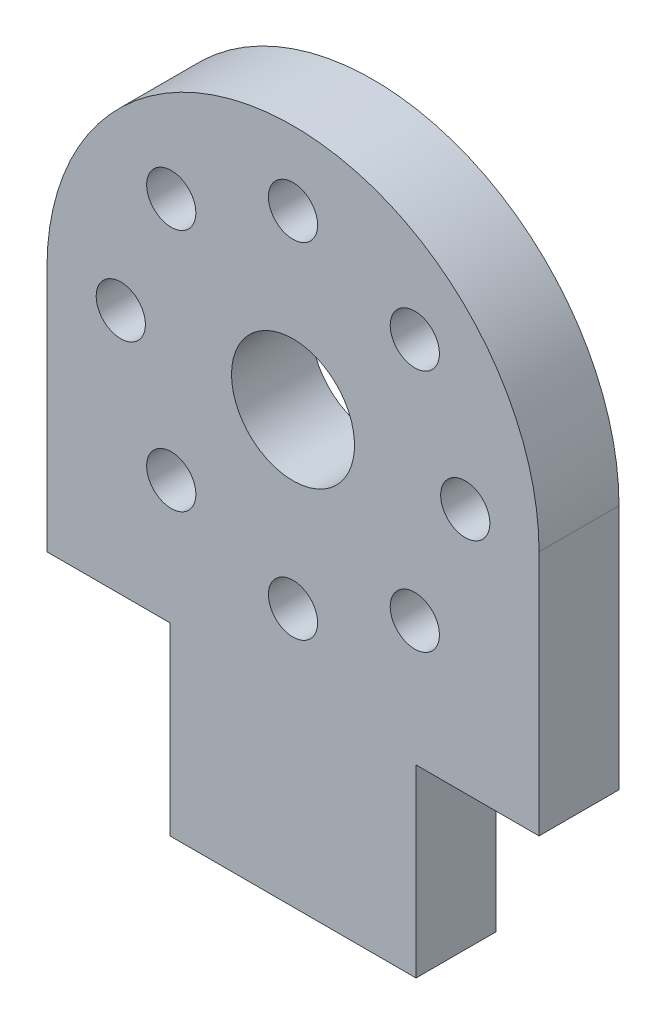
SolidWorks part; units mm, degrees
ref_plane "Plan de face" through (0, 0, 0) normal (0, 0, 1) x (1, 0, 0)
ref_plane "Plan de dessus" through (0, 0, 0) normal (0, 1, 0) x (1, 0, 0)
ref_plane "Plan de droite" through (0, 0, 0) normal (1, 0, 0) x (0, 0, -1)
sketch "Esquisse1" plane through (0, 0, 0) normal (0, 0, 1) x (1, 0, 0)
  line L1 (20, -20) -> (20, -75)
  line L3 (0, 0) -> (0, 23.2042) construction
  line L4 (-20, -20) -> (-20, -75)
  arc A0 (-20, -75) -> (20, -75) centre (0, -75) ccw
  arc A1 (20, -20) -> (-20, -20) centre (0, -20) ccw
  circle A2 centre (0, -75) radius 15
  circle A3 centre (0, -20) radius 5
  circle A4 centre (-14, -20) radius 2
  circle A5 centre (-9.8995, -10.1005) radius 2
  circle A6 centre (0, -6) radius 2
  circle A7 centre (9.8995, -10.1005) radius 2
  circle A8 centre (14, -20) radius 2
  circle A9 centre (9.8995, -29.8995) radius 2
  circle A10 centre (0, -34) radius 2
  circle A11 centre (-9.8995, -29.8995) radius 2
  dimension "D1" = 30
extrude "Extrusion1" add sketch "Esquisse1" along normal blind 6.5
sketch "Esquisse2" plane through (0, 0, 6.5) normal (0, 0, 1) x (1, 0, 0)
  line L1 (12, -59) -> (-12, -59)
  arc A0 (-12, -59) -> (12, -59) centre (0, -75) ccw
  circle A1 centre (0, -75) radius 9
  circle A3 centre (0, -62) radius 1.5
  circle A4 centre (0, -88) radius 1.5
  circle A5 centre (-13, -75) radius 1.5
  circle A6 centre (13, -75) radius 1.5
extrude "Extrusion2" add sketch "Esquisse2" along normal blind 30
sketch "Esquisse3" plane through (0, 0, 6.5) normal (0, 0, -1) x (-1, 0, 0)
  circle A0 centre (0, -75) radius 15
extrude "Extrusion3" cut sketch "Esquisse3" against normal blind 27
sketch "Esquisse4" plane through (0, 0, 0) normal (1, 0, 0) x (0, 0, -1)
  line L0 (-36.5, -95) -> (-30, -95)
  line L1 (-36.5, -95) -> (0, -95) construction
  line L2 (-36.5, -95) -> (-36.5, -90)
  line L3 (-36.5, -59) -> (-36.5, -95) construction
  line L4 (-36.5, -90) -> (-30, -95)
extrude "Extrusion4" cut sketch "Esquisse4" against normal through all and the other way through all
sketch "Esquisse5" plane through (0, 0, 36.5) normal (0, 0, 1) x (1, 0, 0)
  line L0 (20, -55) -> (-20, -55)
  line L1 (-20, -20) -> (-20, -75) construction
  line L2 (20, -55) -> (20, -75)
  line L3 (20, -75) -> (20, -20) construction
  line L4 (-20, -55) -> (-20, -75)
  arc A0 (-20, -75) -> (20, -75) centre (0, -75) ccw
extrude "Extrusion5" cut sketch "Esquisse5" against normal through all
sketch "Esquisse6" plane through (0, 0, 6.5) normal (0, 0, 1) x (1, 0, 0)
  line L0 (-20, -55) -> (-10, -55)
  line L1 (20, -55) -> (-20, -55) construction
  line L2 (-10, -55) -> (-10, -40)
  line L3 (-10, -40) -> (-20, -40)
  line L4 (-20, -20) -> (-20, -55) construction
  line L5 (-20, -40) -> (-20, -55)
  line L6 (20, -55) -> (10, -55)
  line L7 (10, -55) -> (10, -40)
  line L8 (10, -40) -> (20, -40)
  line L9 (20, -55) -> (20, -20) construction
  line L10 (20, -40) -> (20, -55)
extrude "Extrusion6" cut sketch "Esquisse6" against normal through all
